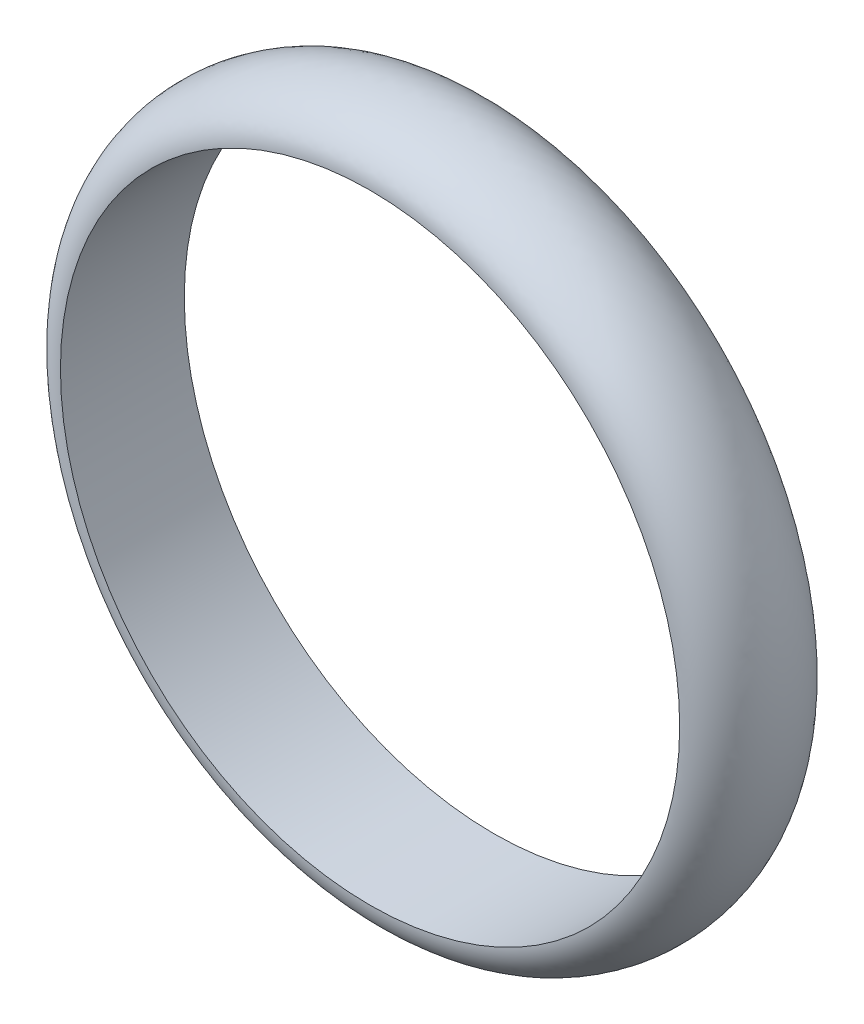
SolidWorks part; units mm, degrees
material "Caoutchouc silicone"
ref_plane "Plan de face" through (0, 0, 0) normal (0, 0, 1) x (1, 0, 0)
ref_plane "Plan de dessus" through (0, 0, 0) normal (0, 1, 0) x (1, 0, 0)
ref_plane "Plan de droite" through (0, 0, 0) normal (1, 0, 0) x (0, 0, -1)
sketch "Esquisse1" plane through (0, 0, 0) normal (1, 0, 0) x (0, 0, -1)
  line L0 (0, 0) -> (41.7903, 0)
  line L1 (-10, 50) -> (10, 50)
  ellipse E0 centre (0, 50) end of major axis (-10, 50) minor radius 7 (-10, 50) -> (10, 50) cw
  dimension "D1" = 20
  dimension "D2" = 10
  dimension "D3" = 50
  dimension "D4" = 7
revolve "Révolution1" add sketch "Esquisse1" angle 360 about L0
